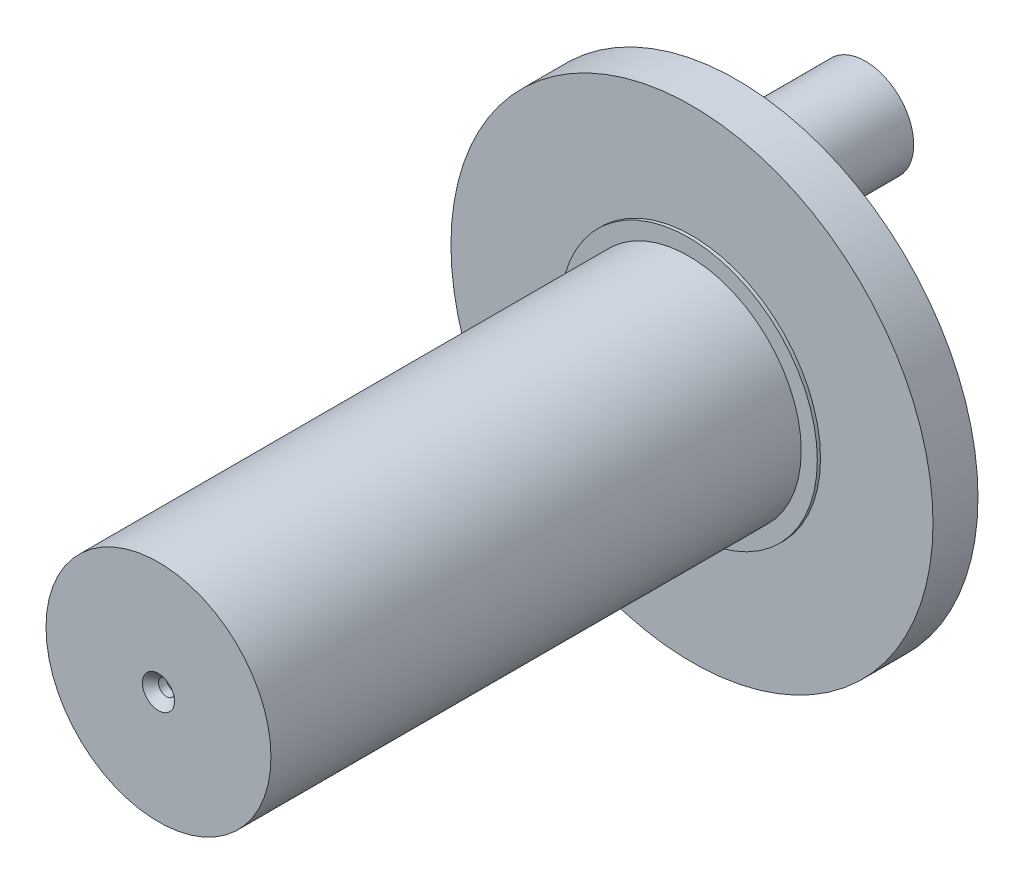
SolidWorks part; units mm, degrees
ref_plane "Front Plane" through (0, 0, 0) normal (0, 0, 1) x (1, 0, 0)
ref_plane "Top Plane" through (0, 0, 0) normal (0, 1, 0) x (1, 0, 0)
ref_plane "Right Plane" through (0, 0, 0) normal (1, 0, 0) x (0, 0, -1)
sketch "Sketch1" plane through (0, 0, 0) normal (0, 0, 1) x (1, 0, 0)
  circle A0 centre (0, 0) radius 15
  dimension "D1" = 30
extrude "Boss-Extrude1" add sketch "Sketch1" along normal blind 2.8
sketch "Sketch3" plane through (0, 0, 2.8) normal (0, 0, 1) x (1, 0, 0)
  circle A0 centre (0, 0) radius 8
  dimension "D1" = 16
extrude "Boss-Extrude3" add sketch "Sketch3" along normal blind 0.2
sketch "Sketch2" plane through (0, 0, 3) normal (0, 0, 1) x (1, 0, 0)
  circle A0 centre (0, 0) radius 7
  dimension "D1" = 14
extrude "Boss-Extrude2" add sketch "Sketch2" along normal blind 33
sketch "Sketch4" plane through (0, 0, 0) normal (0, 0, -1) x (-1, 0, 0)
  circle A0 centre (0, 9) radius 5
  dimension "D1" = 10
  dimension "D2" = 9
extrude "Boss-Extrude4" add sketch "Sketch4" along normal blind 0.4
sketch "Sketch5" plane through (0, 0, 0) normal (0, 0, -1) x (-1, 0, 0)
  circle A0 centre (0, 9) radius 3
  dimension "D1" = 6
extrude "Boss-Extrude5" add sketch "Sketch5" along normal blind 8
hole_wizard "CSK for M2 Oval Head Machine Screw1" positions "Sketch9" profile "Sketch8" countersink size "M2" standard "ANSI Metric"
sketch "Sketch9" plane through (0, 0, 36) normal (0, 0, 1) x (1, 0, 0)
  point P0 (0, 0)
sketch "Sketch8" plane through (0, 0, 36) normal (1, 0, 0) x (0, -1, 0)
  line L0 (0, 0) -> (0, 1.3004)
  line L1 (0, 1.3004) -> (0.5, 1)
  line L2 (0.5, 1) -> (0.5, 0.5)
  line L3 (0.5, 0.5) -> (1, 0)
  line L5 (1, 0) -> (0, 0)
  line L6 (-0.5, 0.5) -> (-1, 0) construction
  line L10 (0, 1.3004) -> (-0.5, 1) construction
  line L11 (0, -6.35) -> (0, 107.95) construction
  dimension "Hole Dia." = 1
  dimension "Hole Depth" = 1
  dimension "Near C'Sink Dia." = 2
  dimension "Near C'Sink Angle" = 90
  dimension "Drill Angle" = 118
